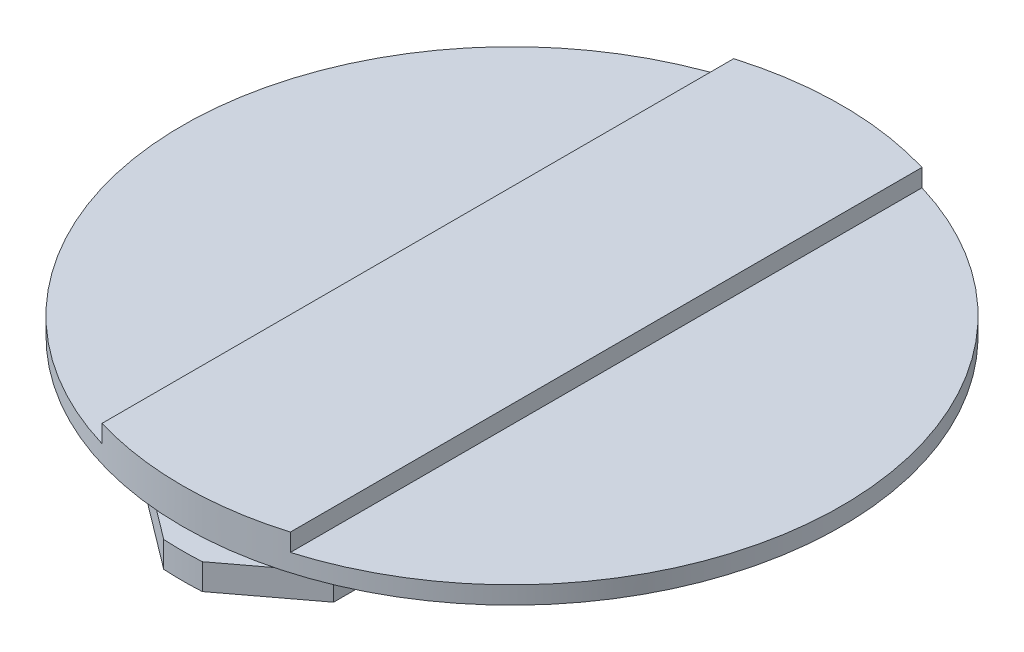
SolidWorks part; units mm, degrees
ref_plane "Спереди" through (0, 0, 0) normal (0, 0, 1) x (1, 0, 0)
ref_plane "Сверху" through (0, 0, 0) normal (0, 1, 0) x (1, 0, 0)
ref_plane "Справа" through (0, 0, 0) normal (1, 0, 0) x (0, 0, -1)
sketch "Эскиз1" plane through (0, 0, 0) normal (0, 0, 1) x (1, 0, 0)
  line L0 (0, 0) -> (0, 7)
  line L1 (0, 7) -> (28, 7)
  line L2 (28, 7) -> (28, 4)
  line L3 (28, 4) -> (24.5, 4)
  line L4 (24.5, 4) -> (24.5, 2.2)
  line L5 (28, 0) -> (0, 0)
  line L6 (0, 16.3116) -> (0, -14.7) construction
  line L7 (24.5, 2.2) -> (28, 2.2)
  line L8 (28, 2.2) -> (28, 0)
  dimension "D1" = 7
  dimension "D2" = 1.8
  dimension "D3" = 28
  dimension "D4" = 3
  dimension "D5" = 24.5
revolve "Повернуть1" add sketch "Эскиз1" angle 360 about L6
sketch "Эскиз2" plane through (0, 0, 0) normal (0, 0, 1) x (1, 0, 0)
  line L0 (8, 7) -> (8, 5.5)
  line L1 (28, 7) -> (-28, 7) construction
  line L2 (8, 5.5) -> (28, 5.5)
  line L4 (28, 5.5) -> (28, 7)
  line L5 (28, 7) -> (8, 7)
  line L6 (-8, 7) -> (-8, 5.5)
  line L7 (-8, 5.5) -> (-28, 5.5)
  line L9 (-28, 5.5) -> (-28, 7)
  line L10 (-28, 7) -> (-8, 7)
  line L11 (8, 0) -> (8, 2.45)
  line L12 (-28, 0) -> (28, 0) construction
  line L13 (8, 2.45) -> (28, 2.45)
  line L14 (28, 2.45) -> (28, 0)
  line L15 (28, 0) -> (8, 0)
  line L16 (-8, 0) -> (-28, 0)
  line L17 (-28, 0) -> (-28, 2.45)
  line L18 (-28, 2.45) -> (-8, 2.45)
  line L19 (-8, 2.45) -> (-8, 0)
  line L20 (28, 2.2) -> (-28, 2.2) construction
  line L21 (28, 0) -> (28, 2.2) construction
  dimension "D1" = 16
  dimension "D2" = 8
  dimension "D3" = 0.25
  dimension "D4" = 1.5
extrude "Вырез-Вытянуть1" cut sketch "Эскиз2" against normal through all and the other way through all
sketch "Эскиз3" plane through (0, 0, 0) normal (0, -1, 0) x (1, 0, 0)
  line L0 (-8, 23.1571) -> (-1.6368, 27.9521)
  line L1 (-8, -23.1571) -> (-8, 23.1571) construction
  line L3 (8, -26.8328) -> (8, 26.8328) construction
  line L4 (-8, -23.1571) -> (-1.6368, -27.9521)
  line L5 (8, -23.1571) -> (1.6368, -27.9521)
  line L6 (1.6368, 27.9521) -> (8, 23.1571)
  arc A0 (8, 26.8328) -> (-8, 26.8328) centre (0, 0) ccw construction
  arc A1 (-8, -26.8328) -> (8, -26.8328) centre (0, 0) ccw construction
  arc M2 (8, 26.8328) -> (-8, 26.8328) centre (0, 0) ccw
  line M3 (-8, 26.8328) -> (-8, -26.8328)
  arc M4 (-8, -26.8328) -> (8, -26.8328) centre (0, 0) ccw
  line M5 (8, -26.8328) -> (8, 26.8328)
  dimension "D1" = 53
extrude "Вырез-Вытянуть2" cut sketch "Эскиз3" against normal up to surface (2.45 mm away) contours L6 M2 M5 | L0 M3 M2 | L4 M3 M4 | L5 M5 M4 up to face at (16.25, 2.45, 0)
